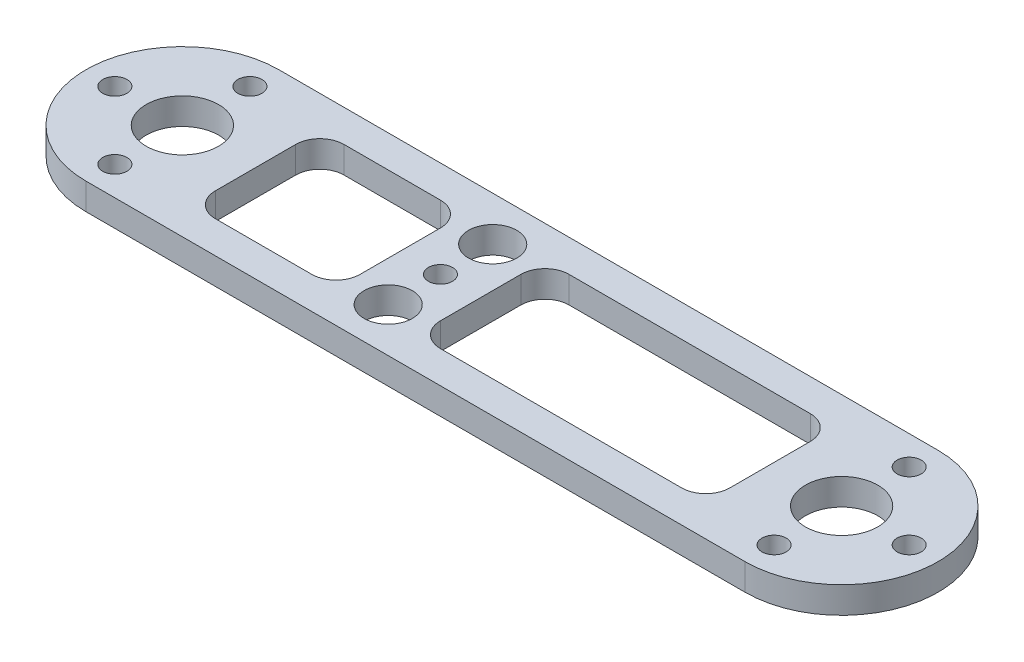
SolidWorks part; units mm, degrees
material "1060 Alloy"
ref_plane "Front Plane" through (0, 0, 0) normal (0, 0, 1) x (1, 0, 0)
ref_plane "Top Plane" through (0, 0, 0) normal (0, 1, 0) x (1, 0, 0)
ref_plane "Right Plane" through (0, 0, 0) normal (1, 0, 0) x (0, 0, -1)
sketch "Sketch1" plane through (0, 0, 0) normal (0, 1, 0) x (1, 0, 0)
  line L0 (-58.3, 0) -> (58.3, 0) construction
  line L1 (41, -12) -> (-41, -12)
  line L2 (53, -12) -> (53, 12) construction
  line L3 (41, 12) -> (-41, 12)
  line L4 (-53, -12) -> (-53, 12) construction
  line L5 (53, -12) -> (-53, 12) construction
  line L6 (53, 12) -> (-53, -12) construction
  line L7 (0, 0) -> (-53, 0) construction
  line L8 (0, 0) -> (0, 12) construction
  line L9 (-8.9, -12) -> (-8.9, 12) construction
  line L10 (-0.9, 8) -> (29.1, 8)
  line L11 (-3.9, 5) -> (-3.9, -5)
  line L12 (-0.9, -8) -> (29.1, -8)
  line L13 (32.1, 5) -> (32.1, -5)
  line L14 (-3.9, 8) -> (32.1, -8) construction
  line L15 (-3.9, -8) -> (32.1, 8) construction
  line L16 (-28.9, 8) -> (-16.9, 8)
  line L17 (-31.9, 5) -> (-31.9, -5)
  line L18 (-28.9, -8) -> (-16.9, -8)
  line L19 (-13.9, 5) -> (-13.9, -5)
  line L20 (-31.9, 8) -> (-13.9, -8) construction
  line L21 (-31.9, -8) -> (-13.9, 8) construction
  arc A0 (-41, 12) -> (-41, -12) centre (-41, 0) ccw
  arc A1 (41, 12) -> (41, -12) centre (41, 0) cw
  circle A2 centre (41, 0) radius 4.5
  circle A3 centre (41, 8.4) radius 1.5
  circle A4 centre (49.4, 0) radius 1.5
  circle A5 centre (41, -8.4) radius 1.5
  circle A6 centre (-41, -8.4) radius 1.5
  circle A7 centre (-49.4, 0) radius 1.5
  circle A8 centre (-41, 8.4) radius 1.5
  circle A9 centre (-41, 0) radius 4.5
  arc A10 (29.1, 8) -> (32.1, 5) centre (29.1, 5) cw
  arc A11 (29.1, -8) -> (32.1, -5) centre (29.1, -5) ccw
  arc A12 (-3.9, -5) -> (-0.9, -8) centre (-0.9, -5) ccw
  arc A13 (-0.9, 8) -> (-3.9, 5) centre (-0.9, 5) ccw
  arc A14 (-31.9, -5) -> (-28.9, -8) centre (-28.9, -5) ccw
  arc A15 (-16.9, -8) -> (-13.9, -5) centre (-16.9, -5) ccw
  arc A16 (-16.9, 8) -> (-13.9, 5) centre (-16.9, 5) cw
  arc A17 (-28.9, 8) -> (-31.9, 5) centre (-28.9, 5) ccw
  circle A18 centre (-8.9, 0) radius 1.5
  circle A19 centre (-8.9, 6.5) radius 3
  circle A20 centre (-8.9, -6.5) radius 3
  point P0 (0, 0)
  point P23 (41, 0)
  point P28 (41, 0)
  point P29 (41, 0)
  point P34 (14.1, 0)
  point P51 (36.5, 0)
  point P52 (-22.9, 0)
  point P75 (-8.9, 9.5)
  dimension "D3" = 12
  dimension "D4" = 9
  dimension "D5" = 3
  dimension "D10" = 3
  dimension "D12" = 16
  dimension "D15" = 3
  dimension "D17" = 3
  dimension "D18" = 6
  dimension "D1" = 106
  dimension "D2" = 24
  dimension "D6" = 8.4
  dimension "D8" = 36
  dimension "D9" = 16
  dimension "D11" = 4.4
  dimension "D13" = 18
  dimension "D14" = 10
  dimension "D16" = 5
  dimension "D19" = 2.5
  dimension "D7" = 3
extrude "Boss-Extrude1" add sketch "Sketch1" along normal blind 3.3
